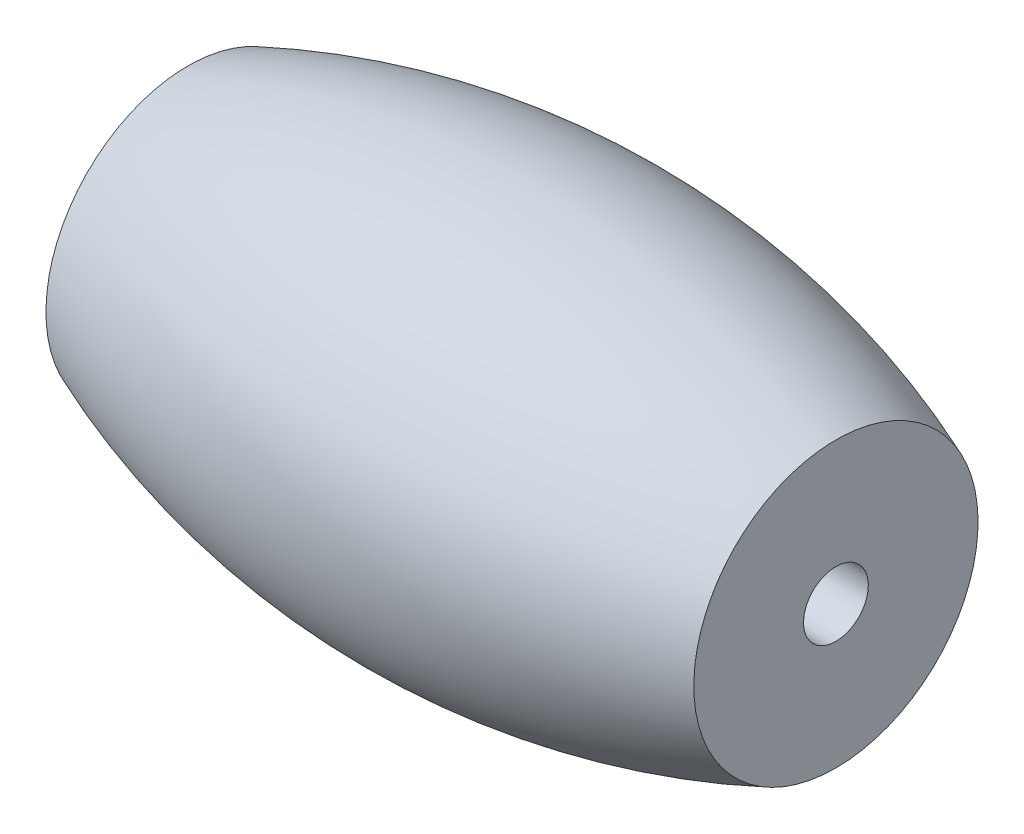
SolidWorks part; units mm, degrees
ref_plane "Plano frontal" through (0, 0, 0) normal (0, 0, 1) x (1, 0, 0)
ref_plane "Plano superior" through (0, 0, 0) normal (0, 1, 0) x (1, 0, 0)
ref_plane "Plano direito" through (0, 0, 0) normal (1, 0, 0) x (0, 0, -1)
sketch "Esboço1" plane through (0, 0, 0) normal (0, 0, 1) x (1, 0, 0)
  line L1 (0, 40) -> (0, 30.5) construction
  line L2 (8.0176, 21.8118) -> (15, 14.2453) construction
  line L4 (-15, 23.919) -> (-15, 37.081) construction
  line L6 (15, 23.919) -> (15, 37.081) construction
  line L7 (-8.7667, 21) -> (-8.0176, 21.8118) construction
  line L8 (0, 30.5) -> (0, 21) construction
  line L9 (-15, 30.5) -> (15, 30.5) construction
  line L10 (-15, 30.5) -> (-15, 37.081)
  line L11 (15, 30.5) -> (15, 37.081)
  line L12 (-15, 30.5) -> (15, 30.5)
  arc A0 (15, 37.081) -> (-15, 37.081) centre (0, 0) ccw
  arc A1 (-15, 23.919) -> (15, 23.919) centre (0, 61) ccw construction
  point P3 (0, 21)
  point P5 (0, 40)
  point P8 (0, 21)
  point P12 (0, 30.5)
  dimension "D1" = 80
  dimension "D2" = 13.162
  dimension "D3" = 80
  dimension "D4" = 13.162
  dimension "D5" = 30
  dimension "D6" = 9.5
revolve "Revolução2" add sketch "Esboço1" angle 360 about L12
sketch "Esboço2" plane through (-15, 0, 0) normal (-1, 0, 0) x (0, 0, 1)
  circle A0 centre (0, 30.5) radius 1.5
  dimension "D1" = 3
extrude "Corte-extrusão1" cut sketch "Esboço2" against normal through all
